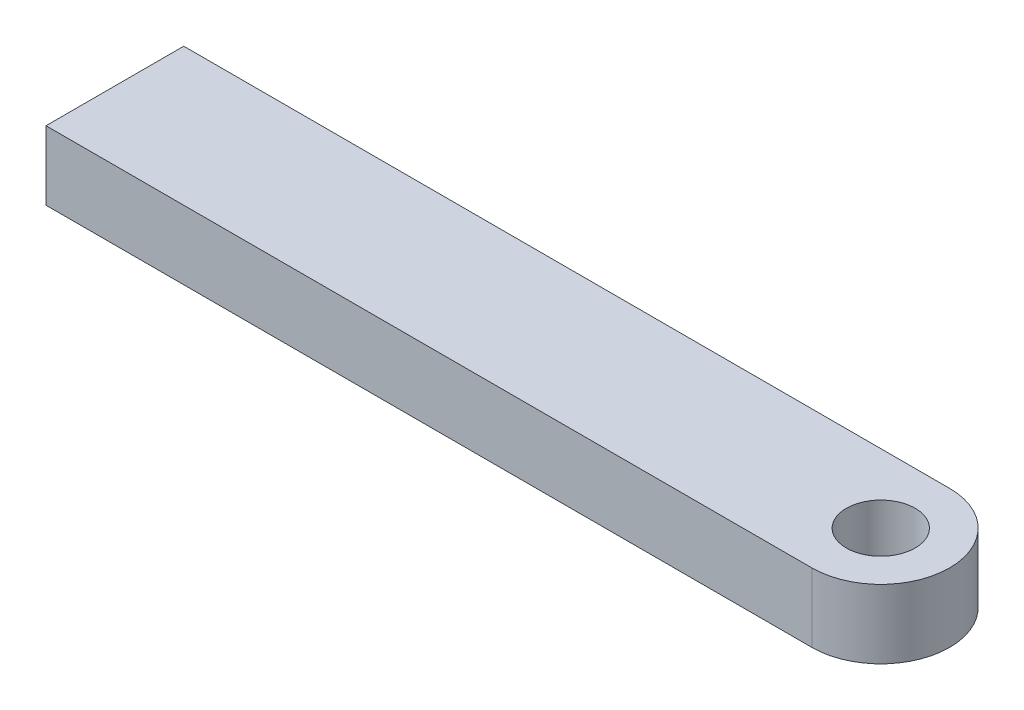
SolidWorks part; units mm, degrees
ref_plane "Plan de face" through (0, 0, 0) normal (0, 0, 1) x (1, 0, 0)
ref_plane "Plan de dessus" through (0, 0, 0) normal (0, 1, 0) x (1, 0, 0)
ref_plane "Plan de droite" through (0, 0, 0) normal (1, 0, 0) x (0, 0, -1)
sketch "Esquisse1" plane through (0, 0, 0) normal (0, 1, 0) x (1, 0, 0)
  line L0 (-55.6, -5) -> (0, -5)
  line L1 (0, 5) -> (-55.6, 5)
  line L2 (-55.6, 5) -> (-55.6, -5)
  arc A0 (0, -5) -> (0, 5) centre (0, 0) ccw
  circle A1 centre (0, 0) radius 2.5
  dimension "D3" = 5
  dimension "D1" = 10
  dimension "D2" = 55.6
  dimension "D4" = 90
extrude "Boss.-Extru.1" add sketch "Esquisse1" along normal mid plane 5
hole_wizard "Trou taraudé M3x0.51" positions "Esquisse3" profile "Esquisse2" tap size "M3x0.5" standard "Ansi Metric"
sketch "Esquisse3" plane through (-55.6, 0, 0) normal (-1, 0, 0) x (0, 0, 1)
  line L0 (-5, -2.5) -> (5, -2.5) construction
  line L1 (0, -2.5) -> (0, -0.25) construction
  point P7 (0, -0.25)
  dimension "D1" = 2.25
sketch "Esquisse2" plane through (-55.6, -0.25, 0) normal (0, 1, 0) x (0, 0, 1)
  line L0 (0, 0) -> (0, 13.2511)
  line L1 (0, 13.2511) -> (1.25, 12.5)
  line L2 (1.25, 12.5) -> (1.25, 0.275)
  line L3 (1.25, 0.275) -> (1.525, 0)
  line L5 (1.525, 0) -> (0, 0)
  line L6 (-1.25, 0.275) -> (-1.525, 0) construction
  line L10 (0, 13.2511) -> (-1.25, 12.5) construction
  line L11 (0, -6.35) -> (0, 107.95) construction
  dimension "Diamètre du trou pour taraudage" = 2.5
  dimension "Profondeur du trou pour taraudage" = 12.5
  dimension "Diamètre du fraisage entrant" = 3.05
  dimension "Angle du fraisage entrant" = 90
  dimension "Angle de pointe" = 118
cosmetic thread "Filetage de perçage1" parameters "D1"=10, "D2"=3
